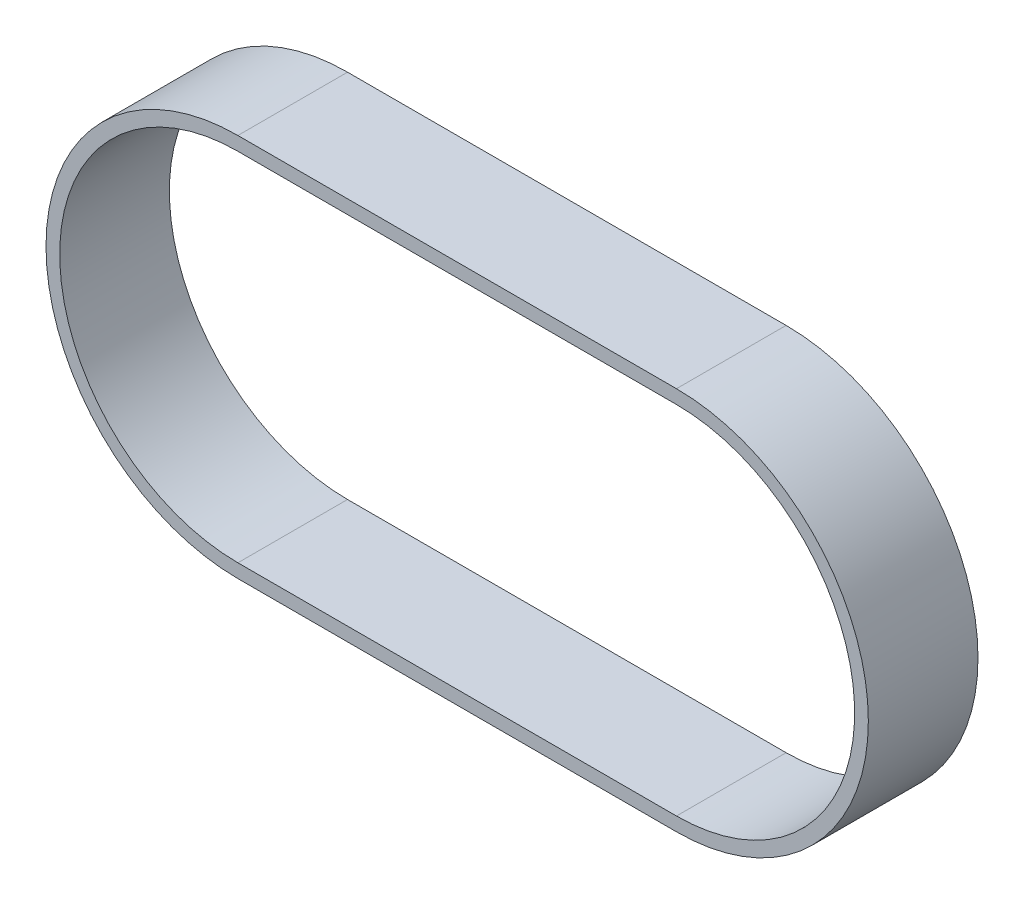
SolidWorks part; units mm, degrees
ref_plane "Plan de face" through (0, 0, 0) normal (0, 0, 1) x (1, 0, 0)
ref_plane "Plan de dessus" through (0, 0, 0) normal (0, 1, 0) x (1, 0, 0)
ref_plane "Plan de droite" through (0, 0, 0) normal (1, 0, 0) x (0, 0, -1)
sketch "Esquisse1" plane through (0, 0, 0) normal (0, 0, 1) x (1, 0, 0)
  line L0 (-62.038, 0) -> (150.8582, 0) construction
  line L1 (0, 35) -> (80, 35)
  line L2 (0, -35) -> (80, -35)
  line L3 (0, 32.5) -> (80, 32.5)
  line L4 (0, -32.5) -> (80, -32.5)
  arc A0 (0, 32.5) -> (0, -32.5) centre (0, 0) ccw
  arc A1 (80, -32.5) -> (80, 32.5) centre (80, 0) ccw
  arc A2 (0, 35) -> (0, -35) centre (0, 0) ccw
  arc A3 (80, -35) -> (80, 35) centre (80, 0) ccw
  dimension "D1" = 65
  dimension "D2" = 65
  dimension "D4" = 70
  dimension "D5" = 70
  dimension "D3" = 80
extrude "Boss.-Extru.1" add sketch "Esquisse1" along normal blind 20
